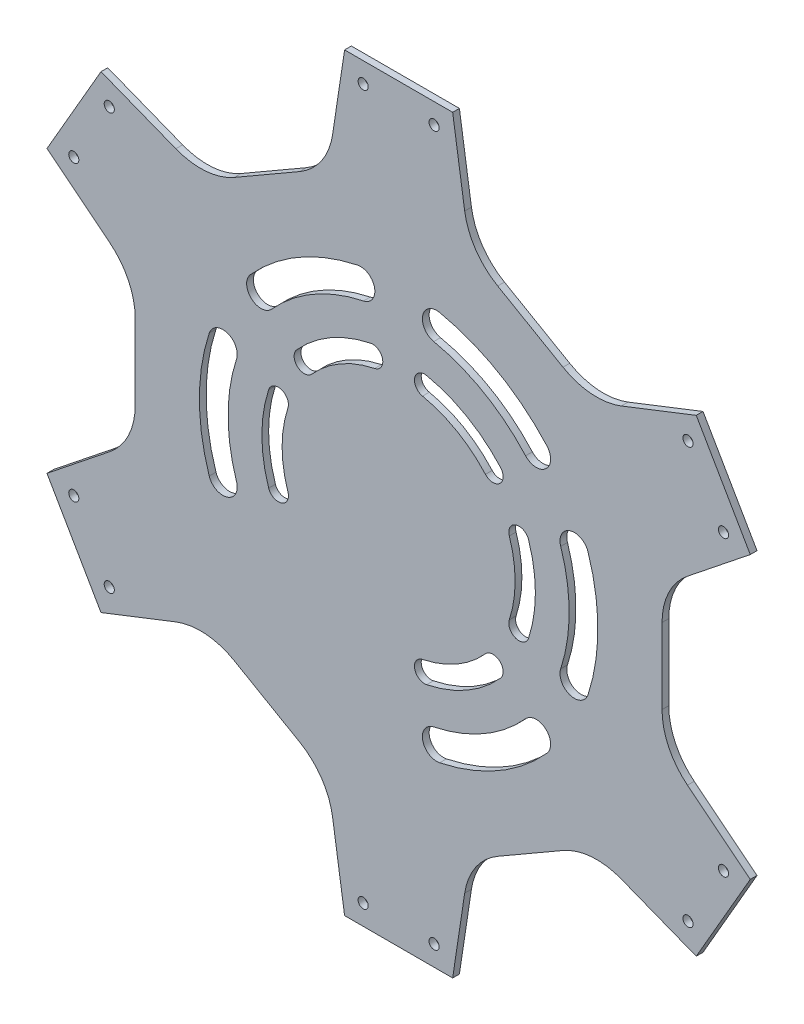
SolidWorks part; units mm, degrees
material "Processing Board, Simple"
ref_plane "Front" through (0, 0, 0) normal (0, 0, 1) x (1, 0, 0)
ref_plane "Top" through (0, 0, 0) normal (0, 1, 0) x (1, 0, 0)
ref_plane "Right" through (0, 0, 0) normal (1, 0, 0) x (0, 0, -1)
sketch "Sketch1" plane through (0, 0, 0) normal (0, 0, 1) x (1, 0, 0)
  line L0 (104.1288, 222) -> (104.1288, 33) construction
  line L1 (208.2576, 152.6436) -> (192.2576, 180.3564)
  line L2 (120.1288, 222) -> (88.1288, 222)
  line L3 (16, 180.3564) -> (0, 152.6436)
  line L4 (0, 69.3564) -> (16, 41.6436)
  line L5 (88.1288, 0) -> (120.1288, 0)
  line L6 (192.2576, 41.6436) -> (208.2576, 69.3564)
  line L7 (152.7932, 172.9703) -> (133.4645, 184.1297)
  line L8 (83.1288, 188.9423) -> (47.1288, 168.1577) construction
  line L9 (26.1288, 131.7846) -> (26.1288, 90.2154) construction
  line L10 (47.1288, 53.8423) -> (83.1288, 33.0577) construction
  line L11 (125.1288, 33.0577) -> (161.1288, 53.8423) construction
  line L12 (182.1288, 99.8406) -> (182.1288, 122.1594)
  line L13 (88.1288, 222) -> (84.5683, 198.4592)
  line L14 (120.1288, 222) -> (123.6894, 198.4592)
  line L15 (192.2576, 180.3564) -> (170.0904, 171.6695)
  line L16 (208.2576, 152.6436) -> (192.2576, 180.3564)
  line L17 (208.2576, 152.6436) -> (189.651, 137.7897)
  line L18 (182.1288, 90.2154) -> (182.1288, 131.7846) construction
  line L19 (161.1288, 168.1577) -> (125.1288, 188.9423) construction
  line L20 (208.2576, 69.3564) -> (189.651, 84.2103)
  line L21 (192.2576, 41.6436) -> (208.2576, 69.3564)
  line L22 (192.2576, 41.6436) -> (170.0904, 50.3305)
  line L23 (133.4645, 37.8703) -> (152.7932, 49.0297)
  line L24 (182.1288, 90.2154) -> (182.1288, 131.7846) construction
  line L25 (120.1288, 0) -> (123.6894, 23.5408)
  line L26 (88.1288, 0) -> (120.1288, 0)
  line L27 (88.1288, 0) -> (84.5683, 23.5408)
  line L28 (55.4645, 49.0297) -> (74.7932, 37.8703)
  line L29 (125.1288, 33.0577) -> (161.1288, 53.8423) construction
  line L30 (16, 41.6436) -> (38.1672, 50.3305)
  line L31 (0, 69.3564) -> (16, 41.6436)
  line L32 (0, 69.3564) -> (18.6066, 84.2103)
  line L33 (26.1288, 122.1594) -> (26.1288, 99.8406)
  line L34 (47.1288, 53.8423) -> (83.1288, 33.0577) construction
  line L35 (0, 152.6436) -> (18.6066, 137.7897)
  line L36 (16, 180.3564) -> (0, 152.6436)
  line L37 (16, 180.3564) -> (38.1672, 171.6695)
  line L38 (74.7932, 184.1297) -> (55.4645, 172.9703)
  line L39 (26.1288, 131.7846) -> (26.1288, 90.2154) construction
  line L40 (0, 0) -> (0, 69.3564) construction
  line L41 (88.1288, 0) -> (0, 0) construction
  arc A0 (123.6894, 198.4592) -> (133.4645, 184.1297) centre (143.4645, 201.4502) ccw
  circle A1 centre (104.1288, 111) radius 78 construction
  arc A2 (170.0904, 171.6695) -> (152.7932, 172.9703) centre (162.7932, 190.2908) cw
  arc A3 (189.651, 137.7897) -> (182.1288, 122.1594) centre (202.1288, 122.1594) ccw
  arc A4 (189.651, 84.2103) -> (182.1288, 99.8406) centre (202.1288, 99.8406) cw
  arc A5 (170.0904, 50.3305) -> (152.7932, 49.0297) centre (162.7932, 31.7092) ccw
  arc A6 (123.6894, 23.5408) -> (133.4645, 37.8703) centre (143.4645, 20.5498) cw
  arc A7 (84.5683, 23.5408) -> (74.7932, 37.8703) centre (64.7932, 20.5498) ccw
  arc A8 (38.1672, 50.3305) -> (55.4645, 49.0297) centre (45.4645, 31.7092) cw
  arc A9 (18.6066, 84.2103) -> (26.1288, 99.8406) centre (6.1288, 99.8406) ccw
  arc A10 (18.6066, 137.7897) -> (26.1288, 122.1594) centre (6.1288, 122.1594) cw
  arc A11 (38.1672, 171.6695) -> (55.4645, 172.9703) centre (45.4645, 190.2908) ccw
  arc A12 (84.5683, 198.4592) -> (74.7932, 184.1297) centre (64.7932, 201.4502) cw
  point P2 (104.1288, 111)
  dimension "D6" = 20
  dimension "D1" = 222
  dimension "D2" = 156
  dimension "D3" = 32
  dimension "D4" = 42
  dimension "D5" = 6
extrude "Boss-Extrude1" add sketch "Sketch1" along normal blind 2 contours L13 A12 L38 A11 L37 L3 L35 A10 L33 A9 L32 L4 L30 A8 L28 A7 L27 L5 L25 A6 L23 A5 L22 L6 L20 A4 L12 A3 L17 L1 L15 A2 L7 A0 L14 L2
sketch "Sketch2" plane through (0, 0, 2) normal (0, 0, 1) x (1, 0, 0)
  line L0 (143.1288, 178.55) -> (65.1288, 43.45) construction
  line L1 (128.2538, 152.7857) -> (135.7538, 165.7761) construction
  line L2 (153.9404, 155.2761) -> (117.5673, 176.2761)
  line L3 (104.1288, 111) -> (130.8818, 95.5541) construction
  line L4 (152.3788, 104.3137) -> (152.3788, 117.6863)
  line L5 (155.3078, 124.7574) -> (163.9646, 133.4142)
  line L6 (167.3788, 90) -> (167.3788, 132)
  line L7 (155.3078, 97.2426) -> (163.9646, 88.5858)
  line L8 (134.0443, 149.4426) -> (122.4633, 156.1289)
  line L9 (122.4633, 65.8711) -> (134.0443, 72.5574)
  line L10 (141.6325, 73.5564) -> (153.458, 70.3878)
  line L11 (117.5673, 45.7239) -> (153.9404, 66.7239)
  line L12 (117.8041, 59.7991) -> (114.6354, 47.9736)
  line L13 (152.7932, 172.9703) -> (133.4645, 184.1297) construction
  line L14 (55.4645, 49.0297) -> (74.7932, 37.8703) construction
  line L15 (117.8041, 162.2009) -> (114.6354, 174.0264)
  line L16 (141.6325, 148.4436) -> (153.458, 151.6122)
  line L17 (104.1288, 111) -> (128.2538, 152.7857) construction
  line L18 (74.2133, 72.5574) -> (85.7943, 65.8711)
  line L19 (90.4536, 59.7991) -> (93.6222, 47.9736)
  line L20 (54.3173, 66.7239) -> (90.6904, 45.7239)
  line L21 (66.6251, 73.5564) -> (54.7996, 70.3878)
  line L22 (55.8788, 117.6863) -> (55.8788, 104.3137)
  line L23 (52.9499, 97.2426) -> (44.293, 88.5858)
  line L24 (40.8788, 132) -> (40.8788, 90)
  line L25 (52.9499, 124.7574) -> (44.293, 133.4142)
  line L26 (85.7943, 156.1289) -> (74.2133, 149.4426)
  line L27 (66.6251, 148.4436) -> (54.7996, 151.6122)
  line L28 (90.6904, 176.2761) -> (54.3173, 155.2761)
  line L29 (90.4536, 162.2009) -> (93.6222, 174.0264)
  arc A0 (152.3788, 117.6863) -> (155.3078, 124.7574) centre (162.3788, 117.6863) cw
  arc A1 (167.3788, 132) -> (163.9646, 133.4142) centre (165.3788, 132) ccw
  arc A2 (153.458, 151.6122) -> (153.9404, 155.2761) centre (152.9404, 153.5441) ccw
  arc A3 (117.5673, 176.2761) -> (114.6354, 174.0264) centre (116.5673, 174.5441) ccw
  arc A4 (134.0443, 149.4426) -> (141.6325, 148.4436) centre (139.0443, 158.1028) ccw
  arc A5 (122.4633, 156.1289) -> (117.8041, 162.2009) centre (127.4633, 164.7891) cw
  arc A6 (163.9646, 88.5858) -> (167.3788, 90) centre (165.3788, 90) ccw
  arc A7 (152.3788, 104.3137) -> (155.3078, 97.2426) centre (162.3788, 104.3137) ccw
  arc A8 (134.0443, 72.5574) -> (141.6325, 73.5564) centre (139.0443, 63.8972) cw
  arc A9 (153.9404, 66.7239) -> (153.458, 70.3878) centre (152.9404, 68.4559) ccw
  arc A10 (114.6354, 47.9736) -> (117.5673, 45.7239) centre (116.5673, 47.4559) ccw
  arc A11 (122.4633, 65.8711) -> (117.8041, 59.7991) centre (127.4633, 57.2109) ccw
  arc A12 (85.7943, 65.8711) -> (90.4536, 59.7991) centre (80.7943, 57.2109) cw
  arc A13 (90.6904, 45.7239) -> (93.6222, 47.9736) centre (91.6904, 47.4559) ccw
  arc A14 (54.7996, 70.3878) -> (54.3173, 66.7239) centre (55.3173, 68.4559) ccw
  arc A15 (74.2133, 72.5574) -> (66.6251, 73.5564) centre (69.2133, 63.8972) ccw
  arc A16 (55.8788, 104.3137) -> (52.9499, 97.2426) centre (45.8788, 104.3137) cw
  arc A17 (40.8788, 90) -> (44.293, 88.5858) centre (42.8788, 90) ccw
  arc A18 (44.293, 133.4142) -> (40.8788, 132) centre (42.8788, 132) ccw
  arc A19 (55.8788, 117.6863) -> (52.9499, 124.7574) centre (45.8788, 117.6863) ccw
  arc A20 (74.2133, 149.4426) -> (66.6251, 148.4436) centre (69.2133, 158.1028) cw
  arc A21 (54.3173, 155.2761) -> (54.7996, 151.6122) centre (55.3173, 153.5441) ccw
  arc A22 (93.6222, 174.0264) -> (90.6904, 176.2761) centre (91.6904, 174.5441) ccw
  arc A23 (85.7943, 156.1289) -> (90.4536, 162.2009) centre (80.7943, 164.7891) ccw
  point P84 (104.1288, 111)
  dimension "D3" = 2
  dimension "D4" = 10
  dimension "D1" = 15
  dimension "D2" = 126.5
  dimension "D5" = 42
  dimension "D6" = 63.25
  dimension "D7" = 6
extrude "Cut-Extrude1" [suppressed] cut sketch "Sketch2" against normal up to next
sketch "Sketch3" plane through (0, 0, 2) normal (0, 0, 1) x (1, 0, 0)
  line L0 (69.3788, 136.25) -> (69.3788, 119.25) construction
  line L1 (72.6288, 136.25) -> (72.6288, 119.25)
  line L2 (66.1288, 136.25) -> (66.1288, 119.25)
  line L3 (84.8788, 140.75) -> (84.8788, 122.25) construction
  line L4 (88.1288, 140.75) -> (88.1288, 122.25)
  line L5 (81.6288, 140.75) -> (81.6288, 122.25)
  line L6 (69.3788, 102.75) -> (69.3788, 85.75) construction
  line L7 (72.6288, 102.75) -> (72.6288, 85.75)
  line L8 (66.1288, 102.75) -> (66.1288, 85.75)
  line L9 (84.8788, 99.75) -> (84.8788, 81.25) construction
  line L10 (88.1288, 99.75) -> (88.1288, 81.25)
  line L11 (81.6288, 99.75) -> (81.6288, 81.25)
  line L12 (104.1288, 222) -> (104.1288, 0) construction
  line L13 (120.1288, 222) -> (88.1288, 222) construction
  line L14 (88.1288, 0) -> (120.1288, 0) construction
  line L15 (26.1288, 111) -> (182.1288, 111) construction
  line L16 (26.1288, 122.1594) -> (26.1288, 99.8406) construction
  line L17 (182.1288, 99.8406) -> (182.1288, 122.1594) construction
  line L18 (88.1288, 131.5) -> (120.1288, 131.5) construction
  line L19 (123.3788, 99.75) -> (123.3788, 81.25) construction
  line L20 (120.1288, 99.75) -> (120.1288, 81.25)
  line L21 (126.6288, 99.75) -> (126.6288, 81.25)
  line L22 (138.8788, 102.75) -> (138.8788, 85.75) construction
  line L23 (135.6288, 102.75) -> (135.6288, 85.75)
  line L24 (142.1288, 102.75) -> (142.1288, 85.75)
  line L25 (123.3788, 140.75) -> (123.3788, 122.25) construction
  line L26 (120.1288, 140.75) -> (120.1288, 122.25)
  line L27 (126.6288, 140.75) -> (126.6288, 122.25)
  line L28 (138.8788, 136.25) -> (138.8788, 119.25) construction
  line L29 (135.6288, 136.25) -> (135.6288, 119.25)
  line L30 (142.1288, 136.25) -> (142.1288, 119.25)
  arc A0 (72.6288, 136.25) -> (66.1288, 136.25) centre (69.3788, 136.25) ccw
  arc A1 (66.1288, 119.25) -> (72.6288, 119.25) centre (69.3788, 119.25) ccw
  arc A2 (88.1288, 140.75) -> (81.6288, 140.75) centre (84.8788, 140.75) ccw
  arc A3 (81.6288, 122.25) -> (88.1288, 122.25) centre (84.8788, 122.25) ccw
  arc A4 (72.6288, 102.75) -> (66.1288, 102.75) centre (69.3788, 102.75) ccw
  arc A5 (66.1288, 85.75) -> (72.6288, 85.75) centre (69.3788, 85.75) ccw
  arc A6 (88.1288, 99.75) -> (81.6288, 99.75) centre (84.8788, 99.75) ccw
  arc A7 (81.6288, 81.25) -> (88.1288, 81.25) centre (84.8788, 81.25) ccw
  arc A8 (120.1288, 99.75) -> (126.6288, 99.75) centre (123.3788, 99.75) cw
  arc A9 (126.6288, 81.25) -> (120.1288, 81.25) centre (123.3788, 81.25) cw
  arc A10 (135.6288, 102.75) -> (142.1288, 102.75) centre (138.8788, 102.75) cw
  arc A11 (142.1288, 85.75) -> (135.6288, 85.75) centre (138.8788, 85.75) cw
  arc A12 (120.1288, 140.75) -> (126.6288, 140.75) centre (123.3788, 140.75) cw
  arc A13 (126.6288, 122.25) -> (120.1288, 122.25) centre (123.3788, 122.25) cw
  arc A14 (135.6288, 136.25) -> (142.1288, 136.25) centre (138.8788, 136.25) cw
  arc A15 (142.1288, 119.25) -> (135.6288, 119.25) centre (138.8788, 119.25) cw
  point P2 (69.3788, 127.75)
  point P7 (84.8788, 131.5)
  point P14 (69.3788, 94.25)
  point P21 (84.8788, 90.5)
  point P40 (84.8788, 119)
  point P41 (84.8788, 103)
  point P42 (69.3788, 106)
  point P43 (69.3788, 116)
  point P44 (69.3788, 139.5)
  point P45 (84.8788, 144)
  point P48 (104.1288, 131.5)
  point P51 (123.3788, 90.5)
  point P58 (138.8788, 94.25)
  point P65 (123.3788, 131.5)
  point P72 (138.8788, 127.75)
  dimension "D1" = 6.5
  dimension "D2" = 9
  dimension "D3" = 10
  dimension "D4" = 16
  dimension "D5" = 23.5
  dimension "D6" = 25
  dimension "D7" = 32
extrude "Cut-Extrude2" [suppressed] cut sketch "Sketch3" against normal up to next
sketch "Sketch4" plane through (0, 0, 2) normal (0, 0, 1) x (1, 0, 0)
  line L0 (104.1288, 222) -> (104.1288, 0) construction
  line L1 (120.1288, 222) -> (88.1288, 222) construction
  line L2 (88.1288, 0) -> (120.1288, 0) construction
  circle A0 centre (92.6288, 216) radius 1.5
  circle A1 centre (115.6288, 216) radius 1.5
  circle A2 centre (96.1288, 196) radius 1.5
  circle A3 centre (112.1288, 196) radius 1.5
  circle A5 centre (173.741, 160.4282) radius 1.5
  circle A6 centre (181.741, 146.5718) radius 1.5
  circle A7 centre (200.8115, 153.5407) radius 1.5
  circle A8 centre (189.3115, 173.4593) radius 1.5
  circle A9 centre (181.741, 75.4282) radius 1.5
  circle A10 centre (173.741, 61.5718) radius 1.5
  circle A11 centre (189.3115, 48.5407) radius 1.5
  circle A12 centre (200.8115, 68.4593) radius 1.5
  circle A13 centre (112.1288, 26) radius 1.5
  circle A14 centre (96.1288, 26) radius 1.5
  circle A15 centre (92.6288, 6) radius 1.5
  circle A16 centre (115.6288, 6) radius 1.5
  circle A17 centre (34.5167, 61.5718) radius 1.5
  circle A18 centre (26.5167, 75.4282) radius 1.5
  circle A19 centre (7.4462, 68.4593) radius 1.5
  circle A20 centre (18.9462, 48.5407) radius 1.5
  circle A21 centre (26.5167, 146.5718) radius 1.5
  circle A22 centre (34.5167, 160.4282) radius 1.5
  circle A23 centre (18.9462, 173.4593) radius 1.5
  circle A24 centre (7.4462, 153.5407) radius 1.5
  point P58 (104.1288, 111)
  dimension "D1" = 3
  dimension "D6" = 6
  dimension "D2" = 23
  dimension "D3" = 16
  dimension "D4" = 20
  dimension "D5" = 6
extrude "Cut-Extrude3" [suppressed] cut sketch "Sketch4" against normal up to next
sketch "Sketch5" plane through (0, 0, 2) normal (0, 0, 1) x (1, 0, 0)
  line L0 (65.1288, 43.45) -> (143.1288, 178.55) construction
  line L1 (55.4645, 49.0297) -> (74.7932, 37.8703) construction
  line L2 (152.7932, 172.9703) -> (133.4645, 184.1297) construction
  arc A0 (134.3029, 138.0144) -> (112.437, 150.6387) centre (104.1288, 111) ccw
  arc A1 (129.8326, 134.0123) -> (111.2061, 144.7663) centre (104.1288, 111) ccw
  arc A2 (116.2891, 168.7332) -> (114.5372, 160.4157) centre (115.4131, 164.5745) ccw
  arc A3 (148.0471, 150.3977) -> (141.7199, 144.7218) centre (144.8835, 147.5598) cw
  arc A4 (141.7199, 144.7218) -> (114.5372, 160.4157) centre (104.1288, 111) ccw
  arc A5 (147.5966, 144.2884) -> (111.2235, 165.2884) centre (104.1288, 111) ccw construction
  arc A6 (148.0471, 150.3977) -> (116.2891, 168.7332) centre (104.1288, 111) ccw
  arc A7 (111.2061, 144.7663) -> (112.437, 150.6387) centre (111.8215, 147.7025) cw
  arc A8 (129.8326, 134.0123) -> (134.3029, 138.0144) centre (132.0677, 136.0133) ccw
  arc A9 (133.9778, 133.7) -> (108.8631, 148.2) centre (104.1288, 111) ccw construction
  arc A10 (136.9099, 100.246) -> (136.9099, 121.754) centre (104.1288, 111) ccw
  arc A11 (136.9099, 121.754) -> (142.611, 123.6243) centre (139.7605, 122.6892) cw
  arc A12 (142.611, 98.3757) -> (142.611, 123.6243) centre (104.1288, 111) ccw
  arc A13 (136.9099, 100.246) -> (142.611, 98.3757) centre (139.7605, 99.3108) ccw
  arc A14 (152.1283, 95.306) -> (152.1283, 126.694) centre (104.1288, 111) ccw
  arc A15 (160.2074, 129.3355) -> (152.1283, 126.694) centre (156.1679, 128.0147) ccw
  arc A16 (160.2074, 92.6645) -> (160.2074, 129.3355) centre (104.1288, 111) ccw
  arc A17 (160.2074, 92.6645) -> (152.1283, 95.306) centre (156.1679, 93.9853) cw
  arc A18 (111.2061, 77.2337) -> (129.8326, 87.9877) centre (104.1288, 111) ccw
  arc A19 (129.8326, 87.9877) -> (134.3029, 83.9856) centre (132.0677, 85.9867) cw
  arc A20 (112.437, 71.3613) -> (134.3029, 83.9856) centre (104.1288, 111) ccw
  arc A21 (111.2061, 77.2337) -> (112.437, 71.3613) centre (111.8215, 74.2975) ccw
  arc A22 (114.5372, 61.5843) -> (141.7199, 77.2782) centre (104.1288, 111) ccw
  arc A23 (148.0471, 71.6023) -> (141.7199, 77.2782) centre (144.8835, 74.4402) ccw
  arc A24 (116.2891, 53.2668) -> (148.0471, 71.6023) centre (104.1288, 111) ccw
  arc A25 (116.2891, 53.2668) -> (114.5372, 61.5843) centre (115.4131, 57.4255) cw
  arc A26 (78.425, 87.9877) -> (97.0515, 77.2337) centre (104.1288, 111) ccw [skipped]
  arc A27 (97.0515, 77.2337) -> (95.8207, 71.3613) centre (96.4361, 74.2975) cw [skipped]
  arc A28 (73.9548, 83.9856) -> (95.8207, 71.3613) centre (104.1288, 111) ccw [skipped]
  arc A29 (78.425, 87.9877) -> (73.9548, 83.9856) centre (76.1899, 85.9867) ccw [skipped]
  arc A30 (66.5377, 77.2782) -> (93.7205, 61.5843) centre (104.1288, 111) ccw [skipped]
  arc A31 (91.9686, 53.2668) -> (93.7205, 61.5843) centre (92.8445, 57.4255) ccw [skipped]
  arc A32 (60.2105, 71.6023) -> (91.9686, 53.2668) centre (104.1288, 111) ccw [skipped]
  arc A33 (60.2105, 71.6023) -> (66.5377, 77.2782) centre (63.3741, 74.4402) cw [skipped]
  arc A34 (71.3477, 121.754) -> (71.3477, 100.246) centre (104.1288, 111) ccw
  arc A35 (71.3477, 100.246) -> (65.6467, 98.3757) centre (68.4972, 99.3108) cw
  arc A36 (65.6467, 123.6243) -> (65.6467, 98.3757) centre (104.1288, 111) ccw
  arc A37 (71.3477, 121.754) -> (65.6467, 123.6243) centre (68.4972, 122.6892) ccw
  arc A38 (56.1293, 126.694) -> (56.1293, 95.306) centre (104.1288, 111) ccw
  arc A39 (48.0502, 92.6645) -> (56.1293, 95.306) centre (52.0898, 93.9853) ccw
  arc A40 (48.0502, 129.3355) -> (48.0502, 92.6645) centre (104.1288, 111) ccw
  arc A41 (48.0502, 129.3355) -> (56.1293, 126.694) centre (52.0898, 128.0147) cw
  arc A42 (97.0515, 144.7663) -> (78.425, 134.0123) centre (104.1288, 111) ccw
  arc A43 (78.425, 134.0123) -> (73.9548, 138.0144) centre (76.1899, 136.0133) cw
  arc A44 (95.8207, 150.6387) -> (73.9548, 138.0144) centre (104.1288, 111) ccw
  arc A45 (97.0515, 144.7663) -> (95.8207, 150.6387) centre (96.4361, 147.7025) ccw
  arc A46 (93.7205, 160.4157) -> (66.5377, 144.7218) centre (104.1288, 111) ccw
  arc A47 (60.2105, 150.3977) -> (66.5377, 144.7218) centre (63.3741, 147.5598) ccw
  arc A48 (91.9686, 168.7332) -> (60.2105, 150.3977) centre (104.1288, 111) ccw
  arc A49 (91.9686, 168.7332) -> (93.7205, 160.4157) centre (92.8445, 164.5745) cw
  point P1 (131.5038, 158.4149)
  point P24 (122.8788, 143.476)
  point P88 (104.1288, 111)
  dimension "D1" = 59
  dimension "D2" = 50.5
  dimension "D3" = 42
  dimension "D4" = 6
  dimension "D5" = 10
  dimension "D6" = 29
  dimension "D7" = 6
extrude "Cut-Extrude4" cut sketch "Sketch5" against normal up to next
sketch "Sketch6" plane through (0, 0, 2) normal (0, 0, 1) x (1, 0, 0)
  line L0 (120.1288, 222) -> (88.1288, 222) construction
  line L1 (104.1288, 222) -> (104.1288, 227.5049) construction
  line L2 (104.1288, 111) -> (94.1173, 128.3405) construction
  line L3 (26.1288, 111) -> (182.1288, 111) construction
  line L4 (26.1288, 122.1594) -> (26.1288, 99.8406) construction
  line L5 (182.1288, 99.8406) -> (182.1288, 122.1594) construction
  line L6 (8, 166.5) -> (200.2576, 55.5) construction
  line L7 (16, 180.3564) -> (0, 152.6436) construction
  line L8 (192.2576, 41.6436) -> (208.2576, 69.3564) construction
  line L9 (8, 55.5) -> (200.2576, 166.5) construction
  line L10 (0, 69.3564) -> (16, 41.6436) construction
  line L11 (208.2576, 152.6436) -> (192.2576, 180.3564) construction
  line L12 (104.1288, 111) -> (114.1404, 128.3405) construction
  circle A0 centre (93.6288, 216) radius 1.5
  circle A1 centre (114.6288, 216) radius 1.5
  circle A2 centre (93.6288, 6) radius 1.5
  circle A3 centre (114.6288, 6) radius 1.5
  circle A4 centre (7.9462, 67.5933) radius 1.5
  circle A5 centre (18.4462, 49.4067) radius 1.5
  circle A6 centre (7.9462, 154.4067) radius 1.5
  circle A7 centre (18.4462, 172.5933) radius 1.5
  circle A8 centre (189.8115, 172.5933) radius 1.5
  circle A9 centre (200.3115, 154.4067) radius 1.5
  circle A10 centre (200.3115, 67.5933) radius 1.5
  circle A11 centre (189.8115, 49.4067) radius 1.5
  point P29 (104.1288, 111)
  dimension "D1" = 21
  dimension "D3" = 3
  dimension "D4" = 21
  dimension "D2" = 210
  dimension "D5" = 21
  dimension "D8" = 210
  dimension "D9" = 210
extrude "Cut-Extrude5" cut sketch "Sketch6" against normal up to next
